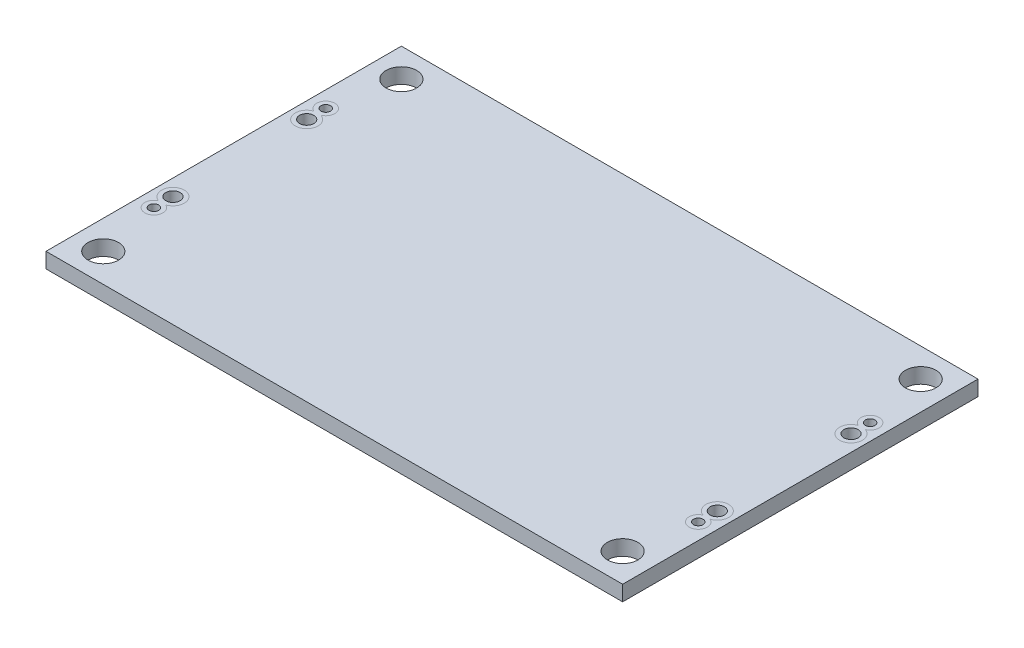
SolidWorks part; units mm, degrees
ref_plane "Front Plane" through (0, 0, 0) normal (0, 0, 1) x (1, 0, 0)
ref_plane "Top Plane" through (0, 0, 0) normal (0, 1, 0) x (1, 0, 0)
ref_plane "Right Plane" through (0, 0, 0) normal (1, 0, 0) x (0, 0, -1)
sketch "Sketch1" plane through (0, 0, 0) normal (0, 1, 0) x (1, 0, 0)
  line L1 (-30.19, 18.605) -> (30.19, 18.605)
  line L2 (-30.19, 18.605) -> (-30.19, -18.605)
  line L3 (-30.19, -18.605) -> (30.19, -18.605)
  line L4 (30.19, 18.605) -> (30.19, -18.605)
  line L5 (-30.19, 18.605) -> (30.19, -18.605) construction
  line L6 (-30.19, -18.605) -> (30.19, 18.605) construction
  point P0 (0, 0)
  dimension "D1" = 37.21
  dimension "D2" = 60.38
extrude "Boss-Extrude1" add sketch "Sketch1" along normal blind 1.6
hole_wizard "M3 Clearance Hole1" positions "Sketch2" profile "Sketch3" hole size "M3" standard "ANSI Metric" end condition through all
sketch "Sketch2" plane through (0, 1.6, 0) normal (0, 1, 0) x (1, 0, 0)
  line L0 (-30.19, 18.605) -> (-30.19, -18.605) construction
  line L1 (30.19, 18.605) -> (-30.19, 18.605) construction
  point P0 (-27.19, 15.605)
  dimension "D1" = 3
  dimension "D2" = 3
sketch "Sketch3" plane through (-27.19, 1.6, -15.605) normal (1, 0, 0) x (0, 0, 1)
  line L0 (0, 0) -> (0, 1.6)
  line L1 (0, 1.6) -> (1.6, 1.6)
  line L2 (1.6, 1.6) -> (1.6, 0)
  line L5 (1.6, 0) -> (0, 0)
  line L11 (0, -6.35) -> (0, 107.95) construction
  dimension "Thru Hole Dia." = 3.2
  dimension "Thru Hole Depth" = 1.6
mirror "Mirror1" about plane through (0, 0, 0) normal (1, 0, 0) of "M3 Clearance Hole1"
mirror "Mirror2" about plane through (0, 0, 0) normal (0, 0, 1) of "Mirror1", "M3 Clearance Hole1"
sketch "Sketch4" plane through (0, 1.6, 0) normal (0, 1, 0) x (1, 0, 0)
  line L1 (-28.5, -7) -> (28.5, -7) construction
  line L2 (-28.5, -7) -> (-28.5, 7) construction
  line L3 (-28.5, 7) -> (28.5, 7) construction
  line L4 (28.5, -7) -> (28.5, 7) construction
  line L5 (-28.5, -7) -> (28.5, 7) construction
  line L6 (-28.5, 7) -> (28.5, -7) construction
  line L7 (-28.5, -9) -> (28.5, -9) construction
  line L8 (-28.5, -9) -> (-28.5, 9) construction
  line L9 (-28.5, 9) -> (28.5, 9) construction
  line L10 (28.5, -9) -> (28.5, 9) construction
  line L11 (-28.5, -9) -> (28.5, 9) construction
  line L12 (-28.5, 9) -> (28.5, -9) construction
  circle A0 centre (28.5, 7) radius 0.75
  circle A1 centre (28.5, -7) radius 0.75
  circle A2 centre (-28.5, -7) radius 0.75
  circle A3 centre (-28.5, 7) radius 0.75
  circle A4 centre (-28.5, 9) radius 0.5
  circle A5 centre (28.5, 9) radius 0.5
  circle A6 centre (28.5, -9) radius 0.5
  circle A7 centre (-28.5, -9) radius 0.5
  point P0 (0, 0)
  point P10 (0, 0)
  dimension "D3" = 1.5
  dimension "D4" = 1
  dimension "D1" = 14
  dimension "D2" = 57
  dimension "D5" = 2
extrude "Cut-Extrude1" cut sketch "Sketch4" against normal through all
sketch "Sketch5" plane through (0, 1.6, 0) normal (0, 1, 0) x (1, 0, 0)
  line L0 (0, 0) -> (0, 4.6217) construction
  line L1 (0, 0) -> (-4.9615, 0) construction
  arc A0 (-28.1327, 8.1289) -> (-28.8673, 8.1289) centre (-28.5, 9) ccw
  arc A1 (-28.8673, 8.1289) -> (-28.1327, 8.1289) centre (-28.5, 7) ccw
  arc A2 (28.8673, 8.1289) -> (28.1327, 8.1289) centre (28.5, 7) cw
  arc A3 (28.1327, 8.1289) -> (28.8673, 8.1289) centre (28.5, 9) cw
  arc A4 (-28.8673, -8.1289) -> (-28.1327, -8.1289) centre (-28.5, -7) cw
  arc A5 (-28.1327, -8.1289) -> (-28.8673, -8.1289) centre (-28.5, -9) cw
  arc A6 (28.1327, -8.1289) -> (28.8673, -8.1289) centre (28.5, -9) ccw
  arc A7 (28.8673, -8.1289) -> (28.1327, -8.1289) centre (28.5, -7) ccw
split "Split1" trim tools "Sketch5" bodies to split 105 resulting bodies 106 107 108 109 110
